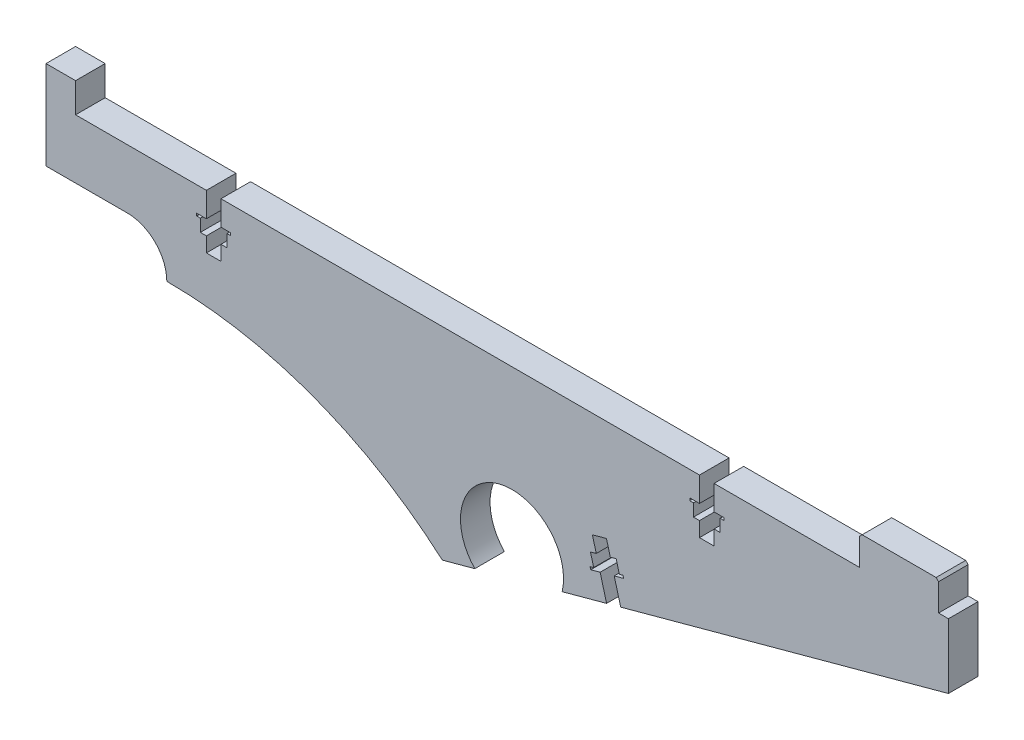
SolidWorks part; units mm, degrees
material "Oak"
ref_plane "Front Plane" through (0, 0, 0) normal (0, 0, 1) x (1, 0, 0)
ref_plane "Top Plane" through (0, 0, 0) normal (0, 1, 0) x (1, 0, 0)
ref_plane "Right Plane" through (0, 0, 0) normal (1, 0, 0) x (0, 0, -1)
sketch "Sketch1" plane through (0, 0, 0) normal (0, 0, 1) x (1, 0, 0)
  line L0 (116.02, 20) -> (116.02, 15)
  line L5 (-16.5, 8) -> (-16.5, 26)
  line L7 (164.5, 26) -> (164.5, 20)
  line L8 (70.4558, -19.231) -> (88.1661, -14.4192) construction
  line L9 (116.02, 15) -> (114.05, 15)
  line L10 (-18, 24.8801) -> (-18, -27.1715) construction
  line L12 (-16.5, 26) -> (-10.5, 26)
  line L13 (114.05, 15) -> (114.05, 14.5)
  line L14 (114.05, 14.5) -> (114.8, 14.5)
  line L15 (114.8, 14.5) -> (114.8, 12)
  line L16 (114.8, 12) -> (116.02, 12)
  line L17 (116.02, 12) -> (116.02, 9)
  line L18 (116.02, 9) -> (118.98, 9)
  line L19 (118.98, 12) -> (118.98, 9)
  line L20 (120.2, 12) -> (118.98, 12)
  line L21 (120.2, 14.5) -> (120.2, 12)
  line L22 (120.95, 14.5) -> (120.2, 14.5)
  line L23 (120.95, 15) -> (120.95, 14.5)
  line L24 (118.98, 15) -> (120.95, 15)
  line L25 (118.98, 20) -> (118.98, 15)
  line L26 (117.5, 20) -> (117.5, 9) construction
  line L27 (88.1661, -14.4192) -> (166.5, 6.8638)
  line L28 (78, -12) -> (79.311, -16.8251) construction
  line L29 (-16.5, 8) -> (0, 8)
  line L30 (17.5, 20) -> (17.5, 9) construction
  line L31 (16.02, 20) -> (16.02, 15)
  line L32 (16.02, 15) -> (14.05, 15)
  line L33 (14.05, 15) -> (14.05, 14.5)
  line L34 (14.05, 14.5) -> (14.8, 14.5)
  line L35 (14.8, 14.5) -> (14.8, 12)
  line L36 (14.8, 12) -> (16.02, 12)
  line L37 (16.02, 12) -> (16.02, 9)
  line L38 (16.02, 9) -> (18.98, 9)
  line L39 (18.98, 12) -> (18.98, 9)
  line L40 (20.2, 12) -> (18.98, 12)
  line L41 (20.2, 14.5) -> (20.2, 12)
  line L42 (20.95, 14.5) -> (20.2, 14.5)
  line L43 (16.02, 20) -> (116.02, 20) construction
  line L44 (164.5, 20) -> (166.5, 20)
  line L45 (-10.5, 26) -> (-10.5, 20)
  line L46 (-10.5, 20) -> (16.02, 20)
  line L47 (166.5, 20) -> (166.5, 6.8638)
  line L48 (63.8707, -21.0201) -> (62.5597, -16.1951) construction
  line L49 (62.5597, -16.1951) -> (78, -12) construction
  line L50 (63.8707, -21.0201) -> (70.4558, -19.231)
  line L51 (20.95, 15) -> (20.95, 14.5)
  line L52 (18.98, 15) -> (20.95, 15)
  line L53 (18.98, 20) -> (18.98, 15)
  line L54 (18.98, 20) -> (116.02, 20)
  line L55 (118.98, 20) -> (148.5, 20)
  line L56 (19.5, -3.7) -> (26.5, -3.7) construction
  line L57 (148.5, 20) -> (148.5, 26)
  line L58 (148.5, 26) -> (164.5, 26)
  line L59 (19.5, -2.7) -> (26.5, -2.7) construction
  line L60 (19.5, -4.7) -> (26.5, -4.7) construction
  circle A0 centre (0, 0) radius 6 construction
  circle A1 centre (78, -12) radius 6 construction
  arc A2 (88.1661, -14.4192) -> (70.4558, -19.231) centre (78, -12) ccw
  arc A3 (63.8707, -21.0201) -> (8, 0) centre (8, -84.7611) ccw
  arc A4 (19.5, -2.7) -> (19.5, -4.7) centre (19.5, -3.7) ccw construction
  arc A5 (26.5, -4.7) -> (26.5, -2.7) centre (26.5, -3.7) ccw construction
  arc A6 (8, 0) -> (0, 8) centre (0, 0) ccw
  point P56 (23, -3.7)
  dimension "D1" = 12
  dimension "D23" = 20.9
  dimension "D19" = 1
  dimension "D36" = 16
  dimension "D37" = 6
  dimension "D27" = 11
  dimension "D28" = 3
  dimension "D29" = 0.5
  dimension "D30" = 2.5
  dimension "D31" = 2.96
  dimension "D33" = 6.9
  dimension "D34" = 5.4
  dimension "D35" = 28
  dimension "D5" = 78
  dimension "D7" = 12
  dimension "D24" = 5
  dimension "D15" = 100
  dimension "D16" = 2
  dimension "D17" = 16
  dimension "D18" = 7
  dimension "D20" = 3.7
  dimension "D25" = 16.5
  dimension "D4" = 20
  dimension "D6" = 12
  dimension "D8" = 6
  dimension "D9" = 181
  dimension "D14" = 2
extrude "Boss-Extrude1" add sketch "Sketch1" along normal blind 6
chamfer "Chamfer1" [suppressed] distance 3 distance2 2
chamfer "Chamfer2" distance 0.5 angle 45 2 edges at (164.5, 26, 3) (148.5, 26, 3)
sketch "Sketch2" plane through (0, 0, 6) normal (0, 0, 1) x (1, 0, 0)
  line L0 (98.6113, -11.5813) -> (95.7272, -0.9661) construction
  line L1 (88.1661, -14.4192) -> (166.5, 6.8638) construction
  line L2 (100.0395, -11.1932) -> (97.1831, -11.9693)
  line L3 (94.2989, -1.3541) -> (97.1554, -0.578)
  line L4 (97.1554, -0.578) -> (97.942, -3.4731)
  line L5 (97.942, -3.4731) -> (99.1193, -3.1532)
  line L6 (99.1193, -3.1532) -> (99.7748, -5.5658)
  line L7 (99.7748, -5.5658) -> (100.4985, -5.3691)
  line L8 (100.4985, -5.3691) -> (100.6296, -5.8516)
  line L9 (100.6296, -5.8516) -> (98.7285, -6.3681)
  line L10 (98.7285, -6.3681) -> (100.0395, -11.1932)
  line L11 (95.8721, -7.1442) -> (97.1831, -11.9693)
  line L12 (93.971, -7.6607) -> (95.8721, -7.1442)
  line L13 (93.8399, -7.1782) -> (93.971, -7.6607)
  line L14 (94.5637, -6.9816) -> (93.8399, -7.1782)
  line L15 (93.9082, -4.569) -> (94.5637, -6.9816)
  line L16 (95.0855, -4.2492) -> (93.9082, -4.569)
  line L17 (94.2989, -1.3541) -> (95.0855, -4.2492)
  line L18 (78, -12) -> (97.3003, -6.7562) construction
  point P21 (78, -12)
  dimension "D1" = 2.96
  dimension "D2" = 6.9
  dimension "D3" = 5.4
  dimension "D4" = 0.5
  dimension "D5" = 2.5
  dimension "D6" = 3
  dimension "D7" = 11
  dimension "D8" = 20
extrude "Cut-Extrude1" cut sketch "Sketch2" against normal through all
equation "\"bed-plate-thickness\"=6"
equation "\"D1@Boss-Extrude1\"=\"y-cross-rib-thickness\""
equation "\"D37@Sketch1\" = \"bed-plate-thickness\""
equation "\"y-cross-rib-thickness\"=6"
equation "\"y-rib-thickness\"=6"
equation "\"x-plate-thickness\"=5"
equation "\"rod-diameter\"=12"
equation "\"t-nut-hole-diameter\"=3"
equation "\"D20@Sketch1\" = 9 - ( 11.6 / 2 ) + .5"
equation "\"D8@Sketch1\"=\"y-rib-thickness\""
